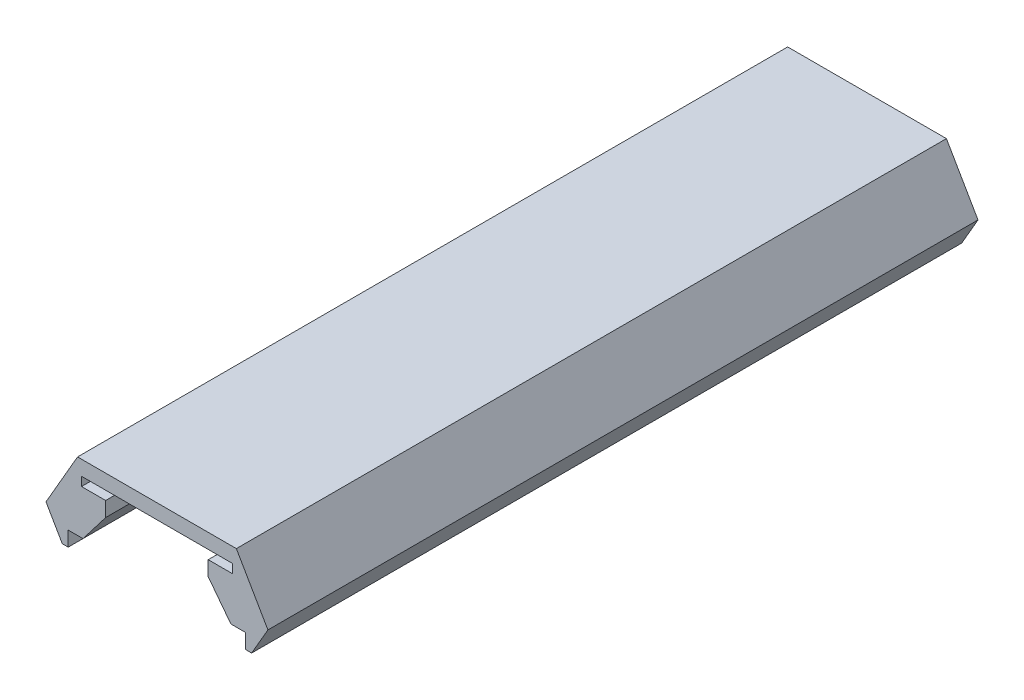
SolidWorks part; units mm, degrees
ref_plane "Front Plane" through (0, 0, 0) normal (0, 0, 1) x (1, 0, 0)
ref_plane "Top Plane" through (0, 0, 0) normal (0, 1, 0) x (1, 0, 0)
ref_plane "Right Plane" through (0, 0, 0) normal (1, 0, 0) x (0, 0, -1)
sketch "Sketch1" plane through (0, 0, 0) normal (0, 0, 1) x (1, 0, 0)
  line L0 (-5.1, 0) -> (5.1, 0)
  line L1 (-5.1, 0) -> (-5.1, -0.6)
  line L2 (-5.1, -0.6) -> (-3.4669, -0.6)
  line L3 (-3.4669, -0.6) -> (-3.4669, -1.6)
  line L4 (-3.4669, -1.6) -> (-5, -3.6)
  line L5 (-5, -3.6) -> (-6, -3.6)
  line L6 (-5.3668, 1) -> (5.3668, 1)
  line L7 (-5.3668, 1) -> (-7.5, -2.6947)
  line L8 (-7.5, -2.6947) -> (-6.4, -4.6)
  line L10 (-6, -4.6) -> (-6, -3.6)
  line L11 (0, -9.7207) -> (0, 9.7207) construction
  line L12 (6, -4.6) -> (6, -3.6)
  line L14 (7.5, -2.6947) -> (6.4, -4.6)
  line L15 (5.3668, 1) -> (7.5, -2.6947)
  line L16 (5, -3.6) -> (6, -3.6)
  line L17 (3.4669, -1.6) -> (5, -3.6)
  line L18 (3.4669, -0.6) -> (3.4669, -1.6)
  line L19 (5.1, -0.6) -> (3.4669, -0.6)
  line L20 (5.1, 0) -> (5.1, -0.6)
  line L21 (-6.4, -4.6) -> (-6, -4.6)
  line L22 (6, -4.6) -> (6.4, -4.6)
  point P3 (-7.5192, -2.8363)
  point P4 (0, 0)
  point P5 (-7.4925, -2.5624)
  point P18 (-7.5, -2.7539)
  point P19 (0, 0)
  point P25 (0, 1)
sketch "Sketch3" plane through (0, 0, 0) normal (0, 0, 1) x (1, 0, 0)
  line L5 (-7.5, -2.6947) -> (-6.4, -4.6) construction
  line L6 (7.5, -2.6947) -> (6.4, -4.6) construction
  line L7 (5.3668, 1) -> (7.5, -2.6947) construction
  line L8 (-5.3668, 1) -> (5.3668, 1) construction
  line L9 (-5.3668, 1) -> (-7.5, -2.6947) construction
  line L10 (7.7309, -2.6947) -> (6.5732, -4.7)
  line L11 (5.4823, 1.2) -> (7.7309, -2.6947)
  line L12 (-5.4823, 1.2) -> (5.4823, 1.2)
  line L13 (-5.4823, 1.2) -> (-7.7309, -2.6947)
  line L14 (-7.7309, -2.6947) -> (-6.5732, -4.7)
  line L15 (-6.5732, -4.7) -> (6.5732, -4.7)
  line L17 (0, -9.7207) -> (0, 9.7207) construction
  line L18 (-6.9, -10.9381) -> (6.9, -10.9381)
  line L19 (0, -10.9381) -> (0, -3.7) construction
  circle A0 centre (0, -3.7) radius 10 construction
  arc A1 (-6.9, -10.9381) -> (6.9, -10.9381) centre (0, -3.7) cw
  point P18 (0, -13.7)
sketch "Sketch2" plane through (0, 0, 0) normal (0, 0, 1) x (1, 0, 0)
  line L20 (7.5, -2.6947) -> (5.3668, 1)
  line L21 (6.4, -4.6) -> (7.5, -2.6947)
  line L22 (6, -4.6) -> (6.4, -4.6)
  line L23 (6, -3.6) -> (6, -4.6)
  line L24 (5, -3.6) -> (6, -3.6)
  line L25 (3.4669, -1.6) -> (5, -3.6)
  line L26 (3.4669, -0.6) -> (3.4669, -1.6)
  line L27 (5.1, -0.6) -> (3.4669, -0.6)
  line L28 (5.1, 0) -> (5.1, -0.6)
  line L29 (-5.1, 0) -> (5.1, 0)
  line L30 (-5.1, -0.6) -> (-5.1, 0)
  line L31 (-3.4669, -0.6) -> (-5.1, -0.6)
  line L32 (-3.4669, -1.6) -> (-3.4669, -0.6)
  line L33 (-5, -3.6) -> (-3.4669, -1.6)
  line L34 (-6, -3.6) -> (-5, -3.6)
  line L35 (-6, -4.6) -> (-6, -3.6)
  line L36 (-6.4, -4.6) -> (-6, -4.6)
  line L37 (-7.5, -2.6947) -> (-6.4, -4.6)
  line L38 (-5.3668, 1) -> (-7.5, -2.6947)
  line L39 (5.3668, 1) -> (-5.3668, 1)
  line L40 (7.5, -2.6947) -> (5.3668, 1)
  line L41 (6.4, -4.6) -> (7.5, -2.6947)
  line L42 (6, -4.6) -> (6.4, -4.6)
  line L43 (6, -3.6) -> (6, -4.6)
  line L44 (5, -3.6) -> (6, -3.6)
  line L45 (3.4669, -1.6) -> (5, -3.6)
  line L46 (3.4669, -0.6) -> (3.4669, -1.6)
  line L47 (5.1, -0.6) -> (3.4669, -0.6)
  line L48 (5.1, 0) -> (5.1, -0.6)
  line L49 (-5.1, 0) -> (5.1, 0)
  line L50 (-5.1, -0.6) -> (-5.1, 0)
  line L51 (-3.4669, -0.6) -> (-5.1, -0.6)
  line L52 (-3.4669, -1.6) -> (-3.4669, -0.6)
  line L53 (-5, -3.6) -> (-3.4669, -1.6)
  line L54 (-6, -3.6) -> (-5, -3.6)
  line L55 (-6, -4.6) -> (-6, -3.6)
  line L56 (-6.4, -4.6) -> (-6, -4.6)
  line L57 (-7.5, -2.6947) -> (-6.4, -4.6)
  line L58 (-5.3668, 1) -> (-7.5, -2.6947)
  line L59 (5.3668, 1) -> (-5.3668, 1)
  dimension "D1" = 0
extrude "Boss-Extrude1" add sketch "Sketch2" along normal mid plane 48
